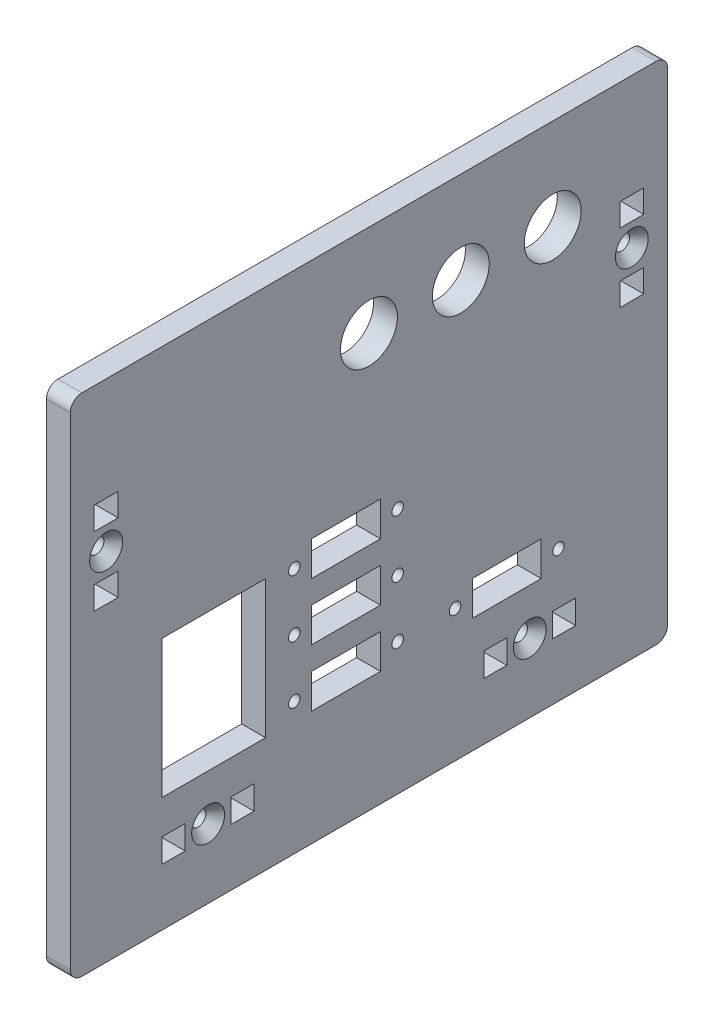
SolidWorks part; units mm, degrees
material "Acrylic (Blue)"
ref_plane "Front Plane" through (0, 0, 0) normal (0, 0, 1) x (1, 0, 0)
ref_plane "Top Plane" through (0, 0, 0) normal (0, 1, 0) x (1, 0, 0)
ref_plane "Right Plane" through (0, 0, 0) normal (1, 0, 0) x (0, 0, -1)
sketch "Sketch1" plane through (0, 0, 0) normal (1, 0, 0) x (0, 0, -1)
  line L0 (82.55, -69.85) -> (-82.55, 69.85) construction
  line L1 (-82.55, 69.85) -> (82.55, 69.85)
  line L2 (-82.55, 69.85) -> (-82.55, -69.85)
  line L3 (-82.55, -69.85) -> (82.55, -69.85)
  line L4 (82.55, 69.85) -> (82.55, -69.85)
  dimension "D1" = 165.1
  dimension "D2" = 139.7
extrude "Boss-Extrude1" add sketch "Sketch1" along normal blind 6.604
sketch "Sketch2" plane through (6.604, 0, 0) normal (1, 0, 0) x (0, 0, -1)
  line L0 (50.8, 44.45) -> (25.4, 44.45) construction
  line L1 (25.4, 44.45) -> (0, 44.45) construction
  line L2 (82.55, 69.85) -> (-82.55, 69.85) construction
  line L3 (-82.55, 69.85) -> (-82.55, -69.85) construction
  line L4 (76.2, 63.5) -> (76.2, -63.5) construction
  line L5 (82.55, -69.85) -> (82.55, 69.85) construction
  line L6 (-76.2, 63.5) -> (-76.2, -63.5) construction
  line L7 (-76.2, -63.5) -> (76.2, -63.5) construction
  line L8 (-76.2, 63.5) -> (76.2, 63.5) construction
  line L9 (-82.55, -69.85) -> (82.55, -69.85) construction
  line L11 (-57.15, -38.1) -> (-28.575, -38.1)
  line L12 (-57.15, -38.1) -> (-57.15, 0)
  line L13 (-57.15, 0) -> (-28.575, 0)
  line L14 (-28.575, -38.1) -> (-28.575, 0)
  circle A0 centre (50.8, 44.45) radius 7.874
  circle A1 centre (25.4, 44.45) radius 7.874
  circle A2 centre (0, 44.45) radius 7.874
  dimension "D1" = 15.748
  dimension "D4" = 25.4
  dimension "D5" = 28.575
  dimension "D6" = 38.1
  dimension "D2" = 25.4
  dimension "D3" = 31.75
  dimension "D7" = 6.35
  dimension "D8" = 6.35
  dimension "D9" = 6.35
  dimension "D10" = 6.35
  dimension "D11" = 31.75
  dimension "D12" = 25.4
extrude "Cut-Extrude1" cut sketch "Sketch2" against normal through all
sketch "Sketch3" plane through (6.604, 0, 0) normal (1, 0, 0) x (0, 0, -1)
  line L0 (-93.8937, -63.5) -> (112.16, -63.5) construction
  line L3 (-82.55, -69.85) -> (82.55, -69.85) construction
  line L4 (-57.15, -47.498) -> (-82.55, -47.498) construction
  line L5 (-82.55, 69.85) -> (-82.55, -69.85) construction
  line L6 (57.15, -47.498) -> (82.55, -47.498) construction
  line L7 (82.55, -69.85) -> (82.55, 69.85) construction
  line B0 (-38.1, -47.498) -> (-31.75, -47.498)
  line B1 (-31.75, -47.498) -> (-31.75, -54.102)
  line B2 (-31.75, -54.102) -> (-38.1, -54.102)
  line B3 (-38.1, -54.102) -> (-38.1, -47.498)
  line B4 (-57.15, -47.498) -> (-50.8, -47.498)
  line B5 (-50.8, -47.498) -> (-50.8, -54.102)
  line B6 (-50.8, -54.102) -> (-57.15, -54.102)
  line B7 (-57.15, -54.102) -> (-57.15, -47.498)
  circle B8 centre (-44.45, -50.8) radius 2.1526
  line B9 (50.8, -47.498) -> (57.15, -47.498)
  line B10 (57.15, -47.498) -> (57.15, -54.102)
  line B11 (57.15, -54.102) -> (50.8, -54.102)
  line B12 (50.8, -54.102) -> (50.8, -47.498)
  line B13 (31.75, -47.498) -> (38.1, -47.498)
  line B14 (38.1, -47.498) -> (38.1, -54.102)
  line B15 (38.1, -54.102) -> (31.75, -54.102)
  line B16 (31.75, -54.102) -> (31.75, -47.498)
  circle B17 centre (44.45, -50.8) radius 2.1526
  dimension "D1" = 19.05
  dimension "D2" = 88.9
  dimension "D3" = 6.35
  dimension "D4" = 9.398
sketch_block_instance "BOLT_HOLE-1"
sketch_block "BOLT_HOLE" parameters "D1"=4.3053, "D2"=6.35, "D3"=6.35, "D4"=6.604
sketch_block_instance "BOLT_HOLE-2"
extrude "Cut-Extrude2" cut sketch "Sketch3" against normal through all
sketch "Sketch4" plane through (6.604, 0, 0) normal (1, 0, 0) x (0, 0, -1)
  line L0 (-20.6375, -33.3375) -> (-15.875, -33.3375) construction
  line L1 (7.9375, -33.3375) -> (3.175, -33.3375) construction
  line L2 (-15.875, -28.575) -> (3.175, -28.575)
  line L3 (-15.875, -28.575) -> (-15.875, -38.1)
  line L4 (-15.875, -38.1) -> (3.175, -38.1)
  line L5 (3.175, -28.575) -> (3.175, -38.1)
  line L6 (-15.875, -33.3375) -> (-6.35, -33.3375) construction
  line L7 (-6.35, -33.3375) -> (3.175, -33.3375) construction
  line L9 (-82.55, 69.85) -> (-82.55, -69.85) construction
  line L10 (-57.15, -38.1) -> (-28.575, -38.1) construction
  circle A0 centre (-20.6375, -33.3375) radius 1.5875
  circle A1 centre (7.9375, -33.3375) radius 1.5875
  dimension "D4" = 3.175
  dimension "D1" = 28.575
  dimension "D2" = 19.05
  dimension "D3" = 9.525
  dimension "D6" = 76.2
extrude "Cut-Extrude3" cut sketch "Sketch4" against normal through all
pattern_linear "LPattern1" count 3 spacing 15.875 along (0, 1, 0) of "Cut-Extrude3"
fillet "Fillet1" radius 3.175 4 edges at (3.302, -69.85, -82.55) (3.302, -69.85, 82.55) (3.302, 69.85, 82.55) (3.302, 69.85, -82.55)
sketch "Sketch5" plane through (6.604, 0, 0) normal (1, 0, 0) x (0, 0, -1)
  line L0 (79.375, 69.85) -> (-79.375, 69.85) construction
  line L3 (-75.946, 41.275) -> (-82.55, 41.275) construction
  line L4 (-82.55, 66.675) -> (-82.55, -66.675) construction
  line L5 (75.946, 41.275) -> (82.55, 41.275) construction
  line L6 (82.55, -66.675) -> (82.55, 66.675) construction
  line B0 (75.946, 22.225) -> (75.946, 15.875)
  line B1 (75.946, 15.875) -> (69.342, 15.875)
  line B2 (69.342, 15.875) -> (69.342, 22.225)
  line B3 (69.342, 22.225) -> (75.946, 22.225)
  line B4 (75.946, 41.275) -> (75.946, 34.925)
  line B5 (75.946, 34.925) -> (69.342, 34.925)
  line B6 (69.342, 34.925) -> (69.342, 41.275)
  line B7 (69.342, 41.275) -> (75.946, 41.275)
  circle B8 centre (72.644, 28.575) radius 2.1526
  line B9 (-75.946, 34.925) -> (-75.946, 41.275)
  line B10 (-75.946, 41.275) -> (-69.342, 41.275)
  line B11 (-69.342, 41.275) -> (-69.342, 34.925)
  line B12 (-69.342, 34.925) -> (-75.946, 34.925)
  line B13 (-75.946, 15.875) -> (-75.946, 22.225)
  line B14 (-75.946, 22.225) -> (-69.342, 22.225)
  line B15 (-69.342, 22.225) -> (-69.342, 15.875)
  line B16 (-69.342, 15.875) -> (-75.946, 15.875)
  circle B17 centre (-72.644, 28.575) radius 2.1526
  dimension "D1" = 28.575
  dimension "D2" = 151.892
sketch_block_instance "BOLT_HOLE-3"
sketch_block_instance "BOLT_HOLE-4"
extrude "Cut-Extrude4" cut sketch "Sketch5" against normal through all
hole_wizard "CSK for #8 Flat Head Socket Cap Screw1" positions "Sketch7" profile "Sketch6" countersink size "#8" standard "ANSI Inch" end condition through all
sketch "Sketch7" plane through (6.604, 0, 0) normal (1, 0, 0) x (0, 0, -1)
  point P0 (-72.644, 28.575)
  point P3 (-44.45, -50.8)
  point P6 (44.45, -50.8)
  point P9 (72.644, 28.575)
sketch "Sketch6" plane through (6.604, 28.575, 72.644) normal (0, 1, 0) x (0, 0, -1)
  line L0 (0, 0) -> (0, 6.604)
  line L1 (0, 6.604) -> (2.1526, 6.604)
  line L2 (2.1526, 6.604) -> (2.1526, 2.7685)
  line L3 (2.1526, 2.7685) -> (4.5593, 0)
  line L5 (4.5593, 0) -> (0, 0)
  line L6 (-2.1526, 2.7685) -> (-4.5593, 0) construction
  line L11 (0, -6.35) -> (0, 107.95) construction
  dimension "Thru Hole Dia." = 4.3053
  dimension "Thru Hole Depth" = 6.604
  dimension "Near C'Sink Dia." = 9.1186
  dimension "Near C'Sink Angle" = 82
pattern_linear "LPattern2" count 2 spacing 44.45 along (0, 0, -1) of "Cut-Extrude3"
other "Move Face1" [suppressed] parameters "D1"=0.0508
